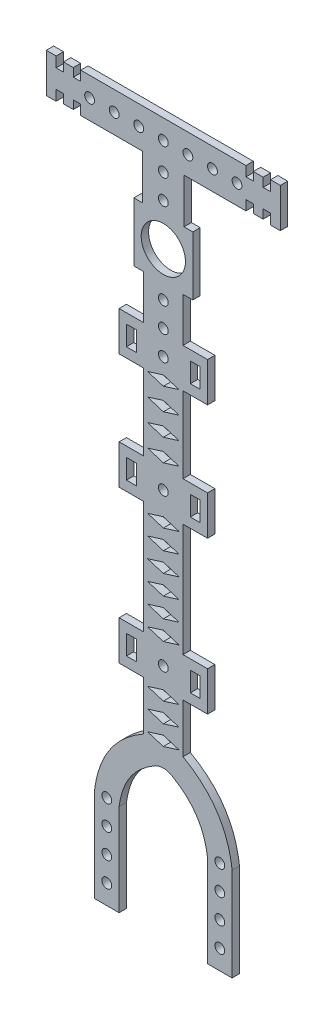
SolidWorks part; units mm, degrees
ref_plane "前视基准面" through (0, 0, 0) normal (0, 0, 1) x (1, 0, 0)
ref_plane "上视基准面" through (0, 0, 0) normal (0, 1, 0) x (1, 0, 0)
ref_plane "右视基准面" through (0, 0, 0) normal (1, 0, 0) x (0, 0, -1)
other "Configuration Table"
sketch "草图1" plane through (0, 0, 0) normal (0, 0, 1) x (1, 0, 0)
  line L0 (0, 1.5) -> (0, -6.2648) construction
  line L1 (0, 0) -> (8.7713, 0) construction
  line L2 (-4.2111, 7) -> (-4.2111, 16.1056)
  line L3 (-6, 7) -> (6, 7)
  line L4 (-6, 7) -> (-6, -5)
  line L5 (-6, -5) -> (6, -5)
  line L6 (6, 7) -> (6, -5)
  line L7 (-6, 7) -> (6, -5) construction
  line L8 (-6, -5) -> (6, 7) construction
  line L9 (-4.2111, 16.1056) -> (-16.8161, 16.1056)
  line L10 (-20.3161, 16.4056) -> (-20.3161, 18.2111)
  line L11 (-21.8161, 24.1056) -> (-23.8161, 24.1056)
  line L12 (21.8161, 16.1056) -> (23.8161, 16.1056)
  line L13 (20.3161, 18.2111) -> (21.8161, 18.2111)
  line L14 (4.2111, 16.1056) -> (4.2111, 7)
  line L15 (-23.8161, 24.1056) -> (-23.8161, 16.1056)
  line L16 (-20.3161, 22) -> (-21.8161, 22)
  line L17 (-21.8161, 22) -> (-21.8161, 24.1056)
  line L18 (-18.3161, 16.4056) -> (-20.3161, 16.4056)
  line L19 (-18.3161, 18.1056) -> (-18.3161, 16.4056)
  line L20 (-16.8161, 18.1056) -> (-18.3161, 18.1056)
  line L21 (21.8161, 18.2111) -> (21.8161, 16.1056)
  line L22 (20.3161, 23.8056) -> (20.3161, 22)
  line L23 (18.3161, 23.8056) -> (20.3161, 23.8056)
  line L24 (18.3161, 22.1056) -> (18.3161, 23.8056)
  line L25 (16.8161, 22.1056) -> (18.3161, 22.1056)
  line L26 (16.8161, 24.1056) -> (16.8161, 22.1056)
  line L27 (-16.8161, 24.1056) -> (16.8161, 24.1056)
  line L28 (-16.8161, 16.1056) -> (-16.8161, 18.1056)
  line L29 (16.8161, 16.1056) -> (16.8161, 18.1056)
  line L30 (16.8161, 16.1056) -> (4.2111, 16.1056)
  line L31 (-25.1648, 20.1056) -> (-15.2017, 20.1056) construction
  line L32 (0, 20.1056) -> (5, 20.1056) construction
  line L33 (0, 20.1056) -> (-5, 20.1056) construction
  line L34 (-4, -14) -> (-4, -5)
  line L35 (-4, -14) -> (-9, -14)
  line L36 (-9, -14) -> (-9, -22)
  line L37 (-9, -22) -> (-4, -22)
  line L38 (-4, -22) -> (-4, -37.5)
  line L39 (-4, -37.5) -> (-9, -37.5)
  line L40 (-9, -37.5) -> (-9, -45.5)
  line L41 (-9, -45.5) -> (-4, -45.5)
  line L42 (-4, -45.5) -> (-4, -68.5)
  line L43 (-4, -68.5) -> (-9, -68.5)
  line L44 (-9, -68.5) -> (-9, -76.5)
  line L45 (-9, -76.5) -> (-4, -76.5)
  line L46 (-4, -76.5) -> (-4, -86.5)
  line L48 (4, -86.5) -> (4, -76.5)
  line L49 (4, -76.5) -> (9, -76.5)
  line L50 (9, -76.5) -> (9, -68.5)
  line L51 (9, -68.5) -> (4, -68.5)
  line L52 (4, -68.5) -> (4, -45.5)
  line L53 (4, -45.5) -> (9, -45.5)
  line L54 (9, -45.5) -> (9, -37.5)
  line L55 (9, -37.5) -> (4, -37.5)
  line L56 (4, -37.5) -> (4, -22)
  line L57 (4, -22) -> (9, -22)
  line L58 (9, -22) -> (9, -14)
  line L59 (9, -14) -> (4, -14)
  line L60 (4, -14) -> (4, -5)
  line L61 (-8.8729, -18) -> (-3.8729, -18) construction
  line L62 (7.5, -20) -> (5.5, -20)
  line L63 (-7.5, -16) -> (-5.5, -16)
  line L64 (-7.5, -16) -> (-7.5, -20)
  line L65 (-7.5, -20) -> (-5.5, -20)
  line L66 (-5.5, -16) -> (-5.5, -20)
  line L67 (-7.5, -16) -> (-5.5, -20) construction
  line L68 (-7.5, -20) -> (-5.5, -16) construction
  line L69 (5.5, -16) -> (5.5, -20)
  line L70 (7.5, -16) -> (5.5, -16)
  line L71 (7.5, -16) -> (7.5, -20)
  line L72 (-4, -29.75) -> (4, -29.75) construction
  line L73 (7.5, -43.5) -> (7.5, -39.5)
  line L74 (7.5, -43.5) -> (5.5, -43.5)
  line L75 (5.5, -43.5) -> (5.5, -39.5)
  line L76 (7.5, -39.5) -> (5.5, -39.5)
  line L77 (-7.5, -39.5) -> (-5.5, -39.5)
  line L78 (-5.5, -43.5) -> (-5.5, -39.5)
  line L79 (-7.5, -43.5) -> (-5.5, -43.5)
  line L80 (-7.5, -43.5) -> (-7.5, -39.5)
  line L81 (-4, -57) -> (4, -57) construction
  line L82 (7.5, -70.5) -> (5.5, -70.5)
  line L83 (5.5, -70.5) -> (5.5, -74.5)
  line L84 (7.5, -74.5) -> (5.5, -74.5)
  line L85 (7.5, -70.5) -> (7.5, -74.5)
  line L86 (-7.5, -70.5) -> (-7.5, -74.5)
  line L87 (-7.5, -70.5) -> (-5.5, -70.5)
  line L88 (-5.5, -70.5) -> (-5.5, -74.5)
  line L89 (-7.5, -74.5) -> (-5.5, -74.5)
  line L90 (-14, -101.5) -> (-14, -120.5)
  line L93 (14, -101.5) -> (14, -120.5)
  line L94 (-9, -101.8077) -> (-9, -120.5)
  line L96 (-9, -41.5) -> (9, -41.5) construction
  line L97 (9, -101.8077) -> (9, -120.5)
  line L103 (0, -30.2) -> (-3.2, -31.2)
  line L104 (-3.2, -31.2) -> (0, -32.2)
  line L117 (0, -50.2) -> (-3.2, -51.2)
  line L118 (-3.2, -51.2) -> (0, -52.2)
  line L141 (0, -46.2) -> (-3.2, -47.2)
  line L142 (-3.2, -47.2) -> (0, -48.2)
  line L143 (0, -48.2) -> (3.2, -47.2)
  line L144 (3.2, -47.2) -> (0, -46.2)
  line L145 (0, -52.2) -> (3.2, -51.2)
  line L146 (3.2, -51.2) -> (0, -50.2)
  line L147 (0, -54.2) -> (-3.2, -55.2)
  line L148 (-3.2, -55.2) -> (0, -56.2)
  line L149 (0, -56.2) -> (3.2, -55.2)
  line L150 (3.2, -55.2) -> (0, -54.2)
  line L151 (0, -58.2) -> (-3.2, -59.2)
  line L152 (-3.2, -59.2) -> (0, -60.2)
  line L153 (0, -60.2) -> (3.2, -59.2)
  line L154 (3.2, -59.2) -> (0, -58.2)
  line L155 (0, -62.2) -> (-3.2, -63.2)
  line L156 (-3.2, -63.2) -> (0, -64.2)
  line L157 (0, -64.2) -> (3.2, -63.2)
  line L158 (3.2, -63.2) -> (0, -62.2)
  line L159 (0, -66.2) -> (-3.2, -67.2)
  line L160 (-3.2, -67.2) -> (0, -68.2)
  line L161 (0, -68.2) -> (3.2, -67.2)
  line L162 (3.2, -67.2) -> (0, -66.2)
  line L183 (0, -70.2) -> (-3.2, -71.2) [skipped]
  line L184 (-3.2, -71.2) -> (0, -72.2) [skipped]
  line L185 (0, -72.2) -> (3.2, -71.2) [skipped]
  line L186 (3.2, -71.2) -> (0, -70.2) [skipped]
  line L187 (0, -74.2) -> (-3.2, -75.2) [skipped]
  line L188 (-3.2, -75.2) -> (0, -76.2) [skipped]
  line L189 (0, -76.2) -> (3.2, -75.2) [skipped]
  line L190 (3.2, -75.2) -> (0, -74.2) [skipped]
  line L191 (0, -78.2) -> (-3.2, -79.2) [skipped]
  line L192 (3.2, -79.2) -> (0, -78.2) [skipped]
  line L193 (0, -80.2) -> (3.2, -79.2) [skipped]
  line L194 (-3.2, -79.2) -> (0, -80.2) [skipped]
  line L195 (0, -82.2) -> (-3.2, -83.2) [skipped]
  line L196 (-3.2, -83.2) -> (0, -84.2) [skipped]
  line L197 (0, -84.2) -> (3.2, -83.2) [skipped]
  line L198 (3.2, -83.2) -> (0, -82.2) [skipped]
  line L199 (0, -86.2) -> (-3.2, -87.2) [skipped]
  line L200 (-3.2, -87.2) -> (0, -88.2) [skipped]
  line L201 (0, -88.2) -> (3.2, -87.2) [skipped]
  line L202 (3.2, -87.2) -> (0, -86.2) [skipped]
  line L203 (-16.8161, 24.1056) -> (-16.8161, 22.1056)
  line L206 (0, -76.7) -> (-3.2, -77.7)
  line L207 (-3.2, -77.7) -> (0, -78.7)
  line L208 (0, -78.7) -> (3.2, -77.7)
  line L209 (3.2, -77.7) -> (0, -76.7)
  line L210 (0, -80.7) -> (-3.2, -81.7)
  line L211 (-3.2, -81.7) -> (0, -82.7)
  line L212 (0, -82.7) -> (3.2, -81.7)
  line L213 (3.2, -81.7) -> (0, -80.7)
  line L214 (0, -84.7) -> (-3.2, -85.7)
  line L215 (-3.2, -85.7) -> (0, -86.7)
  line L216 (0, -86.7) -> (3.2, -85.7)
  line L217 (3.2, -85.7) -> (0, -84.7)
  line L218 (0, -34.7) -> (-3.2, -35.7)
  line L219 (-3.2, -35.7) -> (0, -36.7)
  line L220 (0, -36.7) -> (3.2, -35.7)
  line L221 (3.2, -35.7) -> (0, -34.7)
  line L222 (0, -32.2) -> (3.2, -31.2)
  line L223 (3.2, -31.2) -> (0, -30.2)
  line L224 (0, -25.7) -> (-3.2, -26.7)
  line L225 (-3.2, -26.7) -> (0, -27.7)
  line L226 (0, -27.7) -> (3.2, -26.7)
  line L227 (3.2, -26.7) -> (0, -25.7)
  line L228 (0, -21.2) -> (-3.2, -22.2)
  line L229 (-3.2, -22.2) -> (0, -23.2)
  line L230 (0, -23.2) -> (3.2, -22.2)
  line L231 (3.2, -22.2) -> (0, -21.2)
  line L232 (-9, -72.5) -> (9, -72.5) construction
  line L233 (-16.8161, 22.1056) -> (-18.3161, 22.1056)
  line L234 (-18.3161, 22.1056) -> (-18.3161, 23.8056)
  line L235 (-18.3161, 23.8056) -> (-20.3161, 23.8056)
  line L236 (-20.3161, 23.8056) -> (-20.3161, 22)
  line L237 (-21.8161, 18.2111) -> (-21.8161, 16.1056)
  line L238 (-20.3161, 18.2111) -> (-21.8161, 18.2111)
  line L239 (-21.8161, 16.1056) -> (-23.8161, 16.1056)
  line L240 (16.8161, 18.1056) -> (18.3161, 18.1056)
  line L241 (18.3161, 18.1056) -> (18.3161, 16.4056)
  line L242 (18.3161, 16.4056) -> (20.3161, 16.4056)
  line L243 (21.8161, 22) -> (21.8161, 24.1056)
  line L244 (20.3161, 22) -> (21.8161, 22)
  line L245 (23.8161, 24.1056) -> (23.8161, 16.1056)
  line L246 (21.8161, 24.1056) -> (23.8161, 24.1056)
  line L247 (20.3161, 16.4056) -> (20.3161, 18.2111)
  line L248 (-9, -120.5) -> (-14, -120.5)
  line L250 (9, -120.5) -> (14, -120.5)
  line L251 (-11.5, -120.5) -> (-11.5, -103.1492) construction
  circle A0 centre (0, 1) radius 4.5
  circle A1 centre (0, 9.5405) radius 1
  circle A2 centre (0, 14.5405) radius 1
  circle A3 centre (0, 20.1056) radius 1
  circle A4 centre (5, 20.1056) radius 1
  circle A5 centre (10, 20.1056) radius 1
  circle A6 centre (15, 20.1056) radius 1
  circle A7 centre (-5, 20.1056) radius 1
  circle A8 centre (-10, 20.1056) radius 1
  circle A9 centre (-15, 20.1056) radius 1
  circle A10 centre (0, -18) radius 1
  circle A11 centre (0, -13) radius 1
  circle A12 centre (0, -8) radius 1
  circle A13 centre (0, -41.5) radius 1
  circle A16 centre (-11.5, -116.5) radius 1
  circle A17 centre (-11.5, -111.5) radius 1
  circle A20 centre (11.5, -116.5) radius 1
  circle A21 centre (11.5, -111.5) radius 1
  circle A22 centre (0, -72.5) radius 1
  circle A23 centre (-11.5, -106.5) radius 1
  circle A24 centre (-11.5, -101.5) radius 1
  circle A25 centre (11.5, -101.5) radius 1
  circle A26 centre (11.5, -106.5) radius 1
  spline S0 degree 2 poles (-4, -86.5) (-12.8248, -91.4465) (-14, -101.5) knots 0 0 0 1 1 1
  spline S1 degree 2 poles (4, -86.5) (12.8248, -91.4465) (14, -101.5) knots 0 0 0 1 1 1
  spline S3 degree 2 poles (-1.5553, -90.8616) (-4.1241, -92.3241) (-6.7724, -95.3517) (-8.6016, -98.9141) (-9, -101.8077) knots 0 0 0 0.368595 0.614325 0.98292 0.98292 0.98292
  spline S4 degree 2 poles (-1.5553, -90.8616) (0, -90.1523) (1.5553, -90.8616) knots 0 0 0 1 1 1
  spline S9 degree 2 poles (1.5553, -90.8616) (4.1241, -92.3241) (6.7724, -95.3517) (8.6016, -98.9141) (9, -101.8077) knots 0 0 0 0.368595 0.614325 0.98292 0.98292 0.98292
  point P88 (-6.5, -18)
  point P90 (-6.5, -18)
  point P119 (-14, -101.5)
  point P144 (0, -31.2)
  point P148 (0, -47.2)
  point P150 (0, -26.7)
  point P155 (0, -22.2)
  point P157 (0, -75.2)
  point P158 (0, -51.2)
  point P163 (0, -55.2)
  point P168 (0, -59.2)
  point P174 (0, -83.2)
  point P175 (0, -79.2)
  point P176 (0, -35.7)
  point P182 (0, -77.7)
  point P204 (0, -63.2)
  point P209 (0, -67.2)
  point P214 (0, -87.2)
  point P215 (0, -71.2)
  point P220 (0, -81.7)
  point P225 (0, -85.7)
  point P285 (-23.8161, 20.1056)
  point P294 (23.8161, 20.1056)
  dimension "D1" = 9
  dimension "D17" = 2
  dimension "D19" = 2
  dimension "D43" = 2
  dimension "D45" = 2
  dimension "D47" = 2
  dimension "D2" = 12
  dimension "D3" = 12
  dimension "D6" = 19
  dimension "D7" = 8.4223
  dimension "D8" = 3
  dimension "D9" = 1.5
  dimension "D10" = 1.7
  dimension "D11" = 2
  dimension "D12" = 4
  dimension "D21" = 5
  dimension "D23" = 5
  dimension "D25" = 2
  dimension "D27" = 5
  dimension "D28" = 8
  dimension "D31" = 2
  dimension "D32" = 4
  dimension "D33" = 4
  dimension "D34" = 1.5
  dimension "D36" = 23
  dimension "D37" = 10
  dimension "D38" = 10
  dimension "D39" = 15
  dimension "D46" = 4
  dimension "D48" = 2
  dimension "D51" = 6.4
  dimension "D53" = 2
  dimension "D54" = 11
  dimension "D49" = 1.5
  dimension "D50" = 2
  dimension "D18" = 2
  dimension "D20" = 4
  dimension "D22" = 4
  dimension "D44" = 3
extrude "凸台-拉伸1" add sketch "草图1" along normal blind 1.5 contours L242 L247 L13 L21 L12 L245 L246 L243 L244 L22 L23 L24 L25 L26 L27 L203 L233 L234 L235 L236 L16 L17 L11 L15 L239 L237 L238 L10 L18 L19 L20 L28 L9 L2 L3 L14 L30 L29 L240 L241 A9 A8 A7 A6 A5 | L6 L3 L4 L5 A0 | S4 S9 L97 L250 L93 S1 L48 L49 L50 L51 L52 L53 L54 L55 L56 L57 L58 L59 L60 L5 L34 L35 L36 L37 L38 L39 L40 L41 L42 L43 L44 L45 L46 S0 L90 L248 L94 S3 A26 A21 L82 L85 L84 L83 L79 L80 L77
